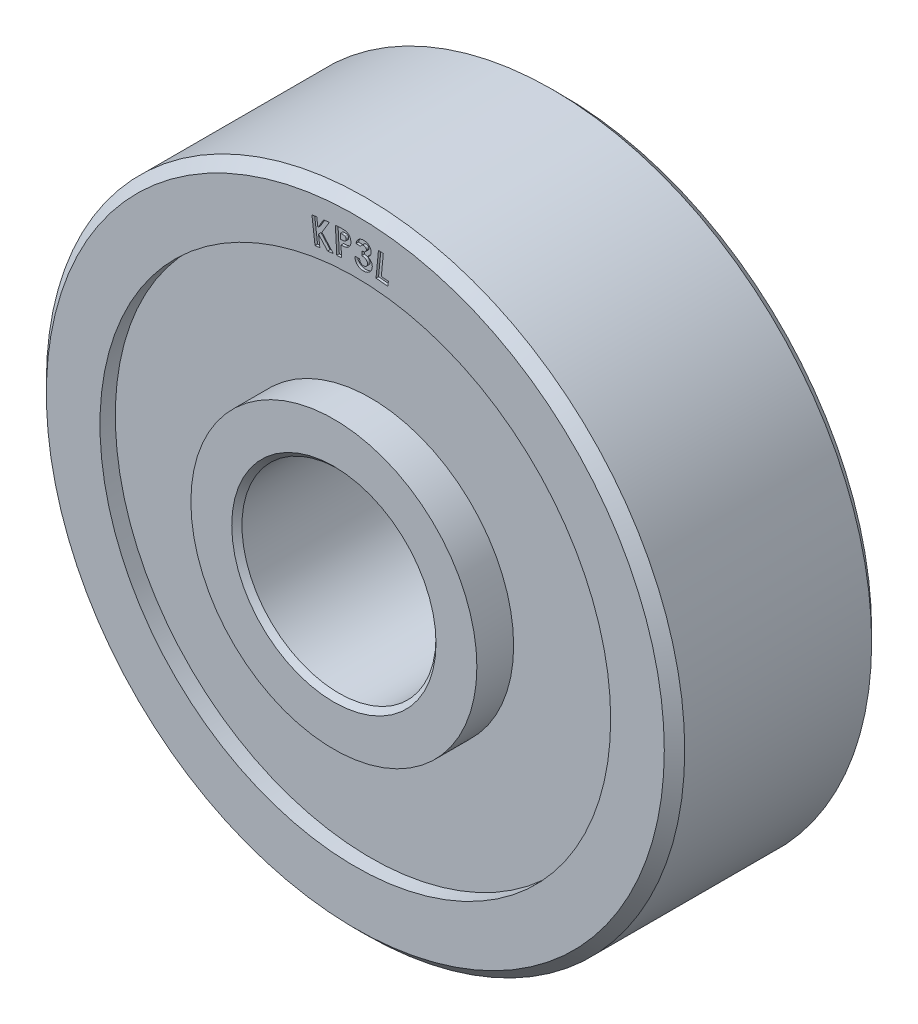
SolidWorks part; units mm, degrees
ref_plane "Front Plane" through (0, 0, 0) normal (0, 0, 1) x (1, 0, 0)
ref_plane "Top Plane" through (0, 0, 0) normal (0, 1, 0) x (1, 0, 0)
ref_plane "Right Plane" through (0, 0, 0) normal (1, 0, 0) x (0, 0, -1)
sketch "Sketch1" plane through (0, 0, 0) normal (1, 0, 0) x (0, 0, -1)
  line L0 (0, 0) -> (63.1482, 0) construction
  line L1 (-3.1115, 2.54) -> (-3.1115, 3.556)
  line L2 (-3.1115, 3.556) -> (-2.1971, 3.556)
  line L3 (-2.1971, 3.556) -> (-2.1971, 6.35)
  line L4 (-2.1971, 6.35) -> (-2.5781, 6.35)
  line L5 (-2.5781, 6.35) -> (-2.5781, 7.6835)
  line L6 (-2.5781, 7.6835) -> (-2.3241, 7.9375)
  line L7 (-2.3241, 7.9375) -> (2.3241, 7.9375)
  line L8 (-2.9845, 2.413) -> (2.9845, 2.413)
  line L9 (0, 0) -> (0, 42.8623) construction
  line L10 (2.5781, 7.6835) -> (2.3241, 7.9375)
  line L11 (2.5781, 6.35) -> (2.5781, 7.6835)
  line L12 (2.1971, 6.35) -> (2.5781, 6.35)
  line L13 (2.1971, 3.556) -> (2.1971, 6.35)
  line L14 (3.1115, 3.556) -> (2.1971, 3.556)
  line L15 (3.1115, 2.54) -> (3.1115, 3.556)
  line L16 (-2.9845, 2.413) -> (-3.1115, 2.54)
  line L17 (2.9845, 2.413) -> (3.1115, 2.54)
  point P3 (-3.1115, 2.413)
  point P19 (3.1115, 2.413)
  dimension "D1" = 4.826
  dimension "D2" = 7.112
  dimension "D3" = 6.223
  dimension "D4" = 5.1562
  dimension "D5" = 0.381
  dimension "D6" = 12.7
  dimension "D7" = 45
  dimension "D8" = 0.254
  dimension "D9" = 15.875
revolve "Revolve1" add sketch "Sketch1" angle 360 about L0
sketch "Sketch2" plane through (0, 0, 2.5781) normal (0, 0, 1) x (1, 0, 0)
  line L0 (0, 0) -> (0, 6.604) construction
  arc A0 (-1.0747, 6.516) -> (1.0747, 6.516) centre (0, 0) cw construction
  text T0 "KP3L" font "Century Gothic" height 0.635
  point P6 (0, 6.604)
  dimension "D2" = 6.604
  dimension "D1" = 2.159
extrude "Cut-Extrude1" cut sketch "Sketch2" against normal blind 0.0635
